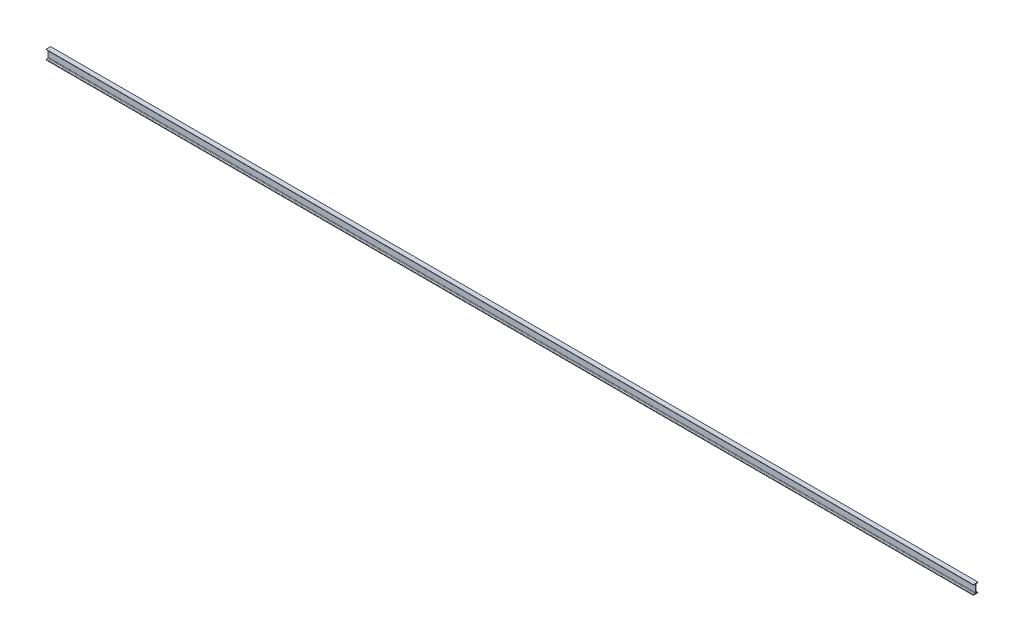
SolidWorks part; units mm, degrees
ref_plane "Front Plane" through (0, 0, 0) normal (0, 0, 1) x (1, 0, 0)
ref_plane "Top Plane" through (0, 0, 0) normal (0, 1, 0) x (1, 0, 0)
ref_plane "Right Plane" through (0, 0, 0) normal (1, 0, 0) x (0, 0, -1)
sketch "Sketch1" plane through (0, 0, 0) normal (0, 0, 1) x (1, 0, 0)
  line L0 (0, 0) -> (12000, 0)
  dimension "D1" = 12000
other "Sb beam 120 X 12(2)"
ref_plane "Plane2" through (0, 0, 0) normal (1, 0, 0) x (0, 0, 1)
sketch "Sketch12" plane through (0, 0, 0) normal (1, 0, 0) x (0, 0, 1)
  line L0 (-30, -60) -> (-30, -58.0801)
  line L1 (-26.6576, -54.1345) -> (-9.1847, -51.2221)
  line L2 (-2.5, -43.331) -> (-2.5, 43.331)
  line L3 (-9.1847, 51.2221) -> (-26.6576, 54.1345)
  line L4 (-30, 58.0801) -> (-30, 60)
  line L5 (-30, 60) -> (30, 60)
  line L6 (30, 60) -> (30, 58.0801)
  line L7 (26.6576, 54.1345) -> (9.1847, 51.2221)
  line L8 (2.5, 43.331) -> (2.5, -43.331)
  line L9 (9.1847, -51.2221) -> (26.6576, -54.1345)
  line L10 (30, -58.0801) -> (30, -60)
  line L11 (30, -60) -> (-30, -60)
  line L15 (-2.5, 0) -> (2.5, 0) construction
  arc A0 (-9.1847, -51.2221) -> (-2.5, -43.331) centre (-10.5, -43.331) ccw
  arc A1 (-2.5, 43.331) -> (-9.1847, 51.2221) centre (-10.5, 43.331) ccw
  arc A2 (9.1847, 51.2221) -> (2.5, 43.331) centre (10.5, 43.331) ccw
  arc A3 (2.5, -43.331) -> (9.1847, -51.2221) centre (10.5, -43.331) ccw
  arc A4 (-26.6576, 54.1345) -> (-30, 58.0801) centre (-26, 58.0801) cw
  arc A5 (26.6576, 54.1345) -> (30, 58.0801) centre (26, 58.0801) ccw
  arc A6 (-30, -58.0801) -> (-26.6576, -54.1345) centre (-26, -58.0801) cw
  arc A7 (30, -58.0801) -> (26.6576, -54.1345) centre (26, -58.0801) ccw
  point P1 (0, 60)
  point P8 (0, -60)
  point P21 (0, 0)
  point P34 (0, 0)
  dimension "RI" = 8
  dimension "D3" = 4
  dimension "BF" = 60
  dimension "D2" = 9.463
  dimension "DEPTH" = 120
  dimension "TW" = 5
  dimension "D1" = 86.662
